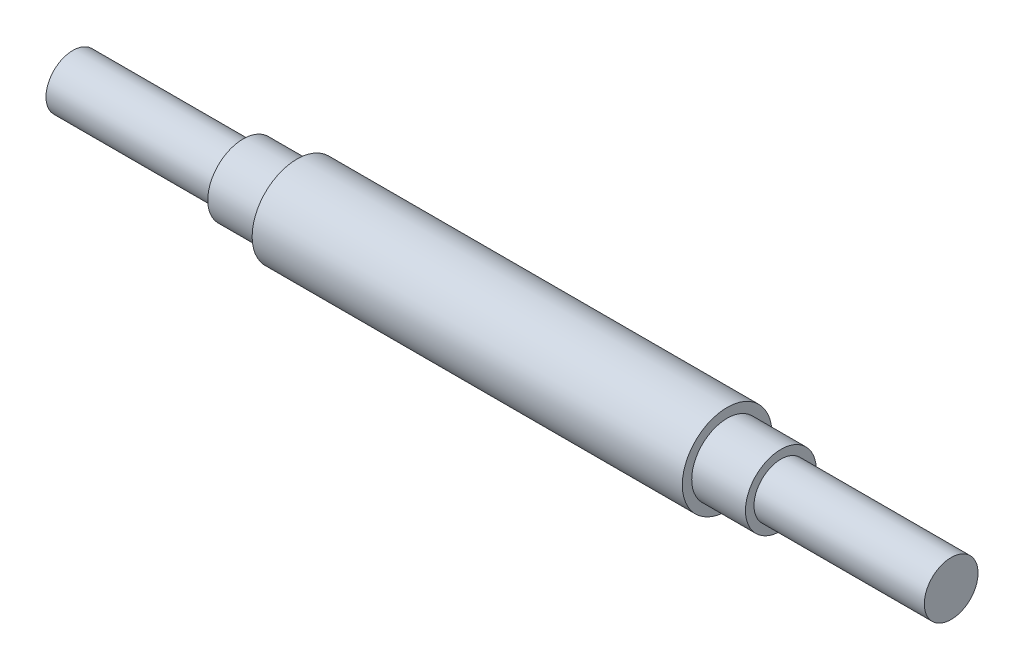
SolidWorks part; units mm, degrees
material "6061 合金"
ref_plane "前视基准面" through (0, 0, 0) normal (0, 0, 1) x (1, 0, 0)
ref_plane "上视基准面" through (0, 0, 0) normal (0, 1, 0) x (1, 0, 0)
ref_plane "右视基准面" through (0, 0, 0) normal (1, 0, 0) x (0, 0, -1)
sketch "草图1" plane through (0, 0, 0) normal (0, 0, 1) x (1, 0, 0)
  line L0 (-47.9121, 0) -> (64.1758, 0) construction
  line L1 (-27.3626, 0) -> (70.6374, 0)
  line L2 (70.6374, 0) -> (70.6374, 3)
  line L3 (70.6374, 3) -> (51.6374, 3)
  line L4 (51.6374, 3) -> (51.6374, 3.95)
  line L5 (51.6374, 3.95) -> (45.6374, 3.95)
  line L6 (45.6374, 3.95) -> (45.6374, 5)
  line L7 (45.6374, 5) -> (-2.3626, 5)
  line L8 (-2.3626, 5) -> (-2.3626, 3.95)
  line L9 (-2.3626, 3.95) -> (-8.3626, 3.95)
  line L10 (-8.3626, 3.95) -> (-8.3626, 3)
  line L11 (-8.3626, 3) -> (-27.3626, 3)
  line L12 (-27.3626, 3) -> (-27.3626, 0)
  dimension "D1" = 48
  dimension "D2" = 6
  dimension "D3" = 19
  dimension "D4" = 3
  dimension "D5" = 3.95
  dimension "D6" = 5
revolve "旋转1" add sketch "草图1" angle 360 about L0
